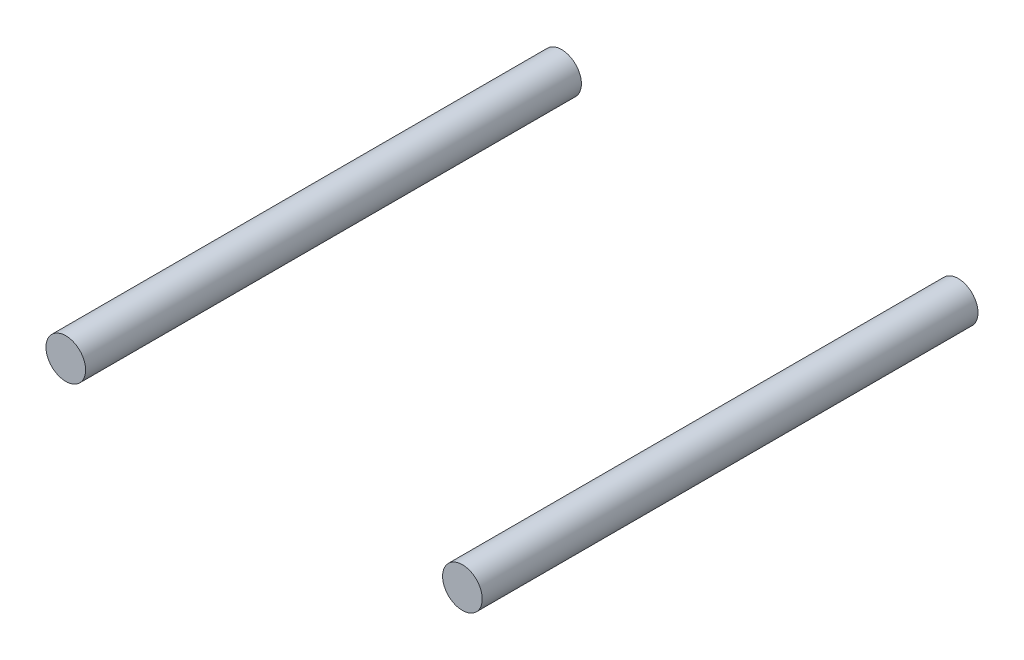
SolidWorks part; units mm, degrees
ref_plane "Front Plane" through (0, 0, 0) normal (0, 0, 1) x (1, 0, 0)
ref_plane "Top Plane" through (0, 0, 0) normal (0, 1, 0) x (1, 0, 0)
ref_plane "Right Plane" through (0, 0, 0) normal (1, 0, 0) x (0, 0, -1)
sketch "Sketch1" plane through (0, 0, 0) normal (0, 0, 1) x (1, 0, 0)
  circle A0 centre (-4, 0) radius 0.4
  circle A1 centre (4, 0) radius 0.4
extrude "Boss-Extrude1" add sketch "Sketch1" along normal mid plane 10
